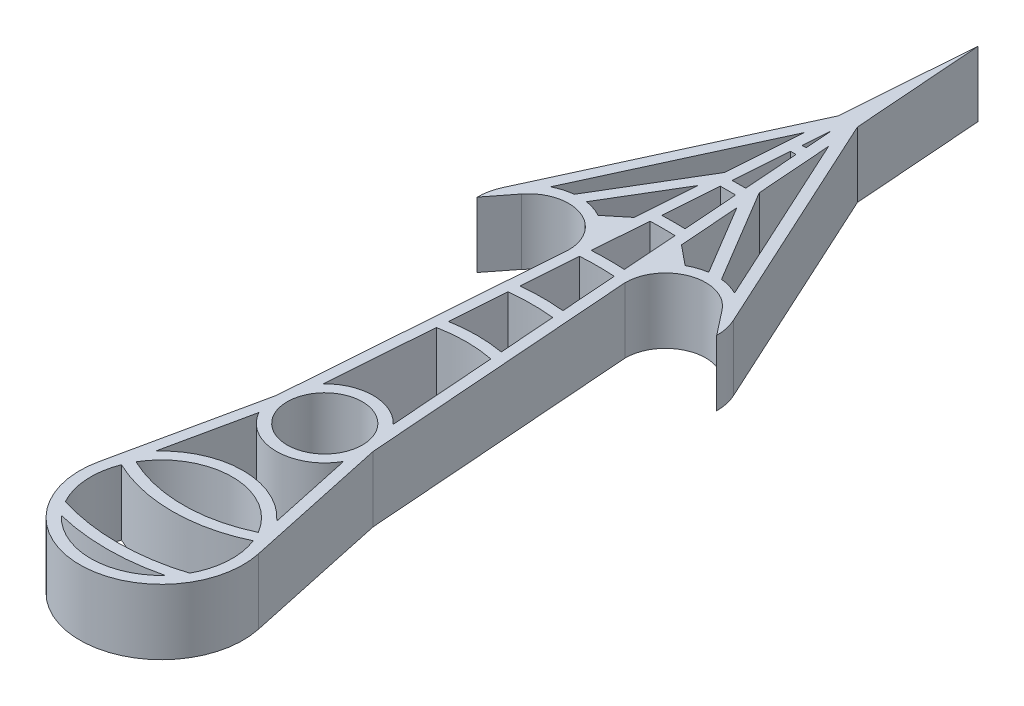
SolidWorks part; units mm, degrees
ref_plane "Front Plane" through (0, 0, 0) normal (0, 0, 1) x (1, 0, 0)
ref_plane "Top Plane" through (0, 0, 0) normal (0, 1, 0) x (1, 0, 0)
ref_plane "Right Plane" through (0, 0, 0) normal (1, 0, 0) x (0, 0, -1)
sketch "Sketch1" plane through (0, 0, 0) normal (0, 1, 0) x (1, 0, 0)
  line L0 (-4.45, 0) -> (0, 60)
  line L1 (0, 60) -> (4.45, 0)
  line L2 (0, 0) -> (0, 60) construction
  line L3 (0, 0) -> (0, -15) construction
  line L4 (-7.3328, -13.4254) -> (-4.45, 0)
  line L5 (4.45, 0) -> (7.3328, -13.4254)
  line L6 (-5.5696, -9.9771) -> (-3.8909, -2.1595)
  line L7 (3.8909, -2.1595) -> (5.5696, -9.9771)
  line L8 (3.45, 0) -> (4.45, 0) construction
  line L13 (-3.2194, 3.0721) -> (0, 46.4798)
  line L20 (0, 46.4798) -> (3.2194, 3.0721)
  circle A0 centre (0, 0) radius 3.45
  circle A2 centre (0, -15) radius 6.5
  arc A3 (5.5696, -9.9771) -> (-5.5696, -9.9771) centre (0, -15) ccw
  arc A8 (-3.8909, -2.1595) -> (3.8909, -2.1595) centre (0, 0) ccw
  arc A9 (3.2194, 3.0721) -> (-3.2194, 3.0721) centre (0, 0) ccw
  arc A11 (-7.3328, -13.4254) -> (7.3328, -13.4254) centre (0, -15) ccw
  circle A12 centre (0, -15) radius 7.5 construction
  point P32 (12.432, 3.8008)
  point P33 (0, 0)
  point P34 (18, 0)
  point P35 (0, 0)
  point P36 (13.3883, 4.0932)
  point P39 (0, 0)
  point P40 (23, 0)
  point P42 (0, 0)
  point P43 (19, 0)
  point P45 (28, 0)
  point P46 (0, 0)
  point P47 (24, 0)
  point P48 (0, 0)
  point P49 (33, 0)
  point P50 (0, 0)
  point P52 (0, 0)
  point P53 (38, 0)
  point P54 (0, 0)
  point P56 (0, 0)
  point P57 (43, 0)
  point P58 (0, 0)
  point P59 (39, 0)
  point P60 (0, 0)
  point P61 (48, 0)
  point P62 (0, 0)
  point P63 (44, 0)
  point P64 (0, 0)
  point P65 (53, 0)
  point P66 (0, 0)
  point P67 (49, 0)
  point P68 (0, 0)
  point P69 (58, 0)
  point P70 (0, 0)
  point P71 (54, 0)
  point P72 (0, 0)
  point P73 (63, 0)
  point P74 (0, 0)
  point P75 (59, 0)
  point P76 (64, 0)
  point P84 (10.5194, -26.7839)
  point P116 (34, 0)
  point P130 (29, 0)
  dimension "D1" = 6.9
  dimension "D3" = 4.45
  dimension "D4" = 15
  dimension "D5" = 1
  dimension "D6" = 13
  dimension "D11" = 4.45
  dimension "D2" = 60
  dimension "D7" = 1
  dimension "D8" = 1
  dimension "D10" = 1
  dimension "D9" = 4.45
extrude "Boss-Extrude1" add sketch "Sketch1" along normal blind 6
sketch "Sketch3" plane through (0, 0, 0) normal (0, 1, 0) x (1, 0, 0)
  line L0 (1.0216, 67.0139) -> (1.0956, 68.0123)
  line L1 (-0.6513, 62.021) -> (-0.5772, 61.0222)
  line L2 (0.5772, 61.0222) -> (0.6513, 62.021)
  line L4 (-3.718, 3.1091) -> (0, 53.2399)
  line L5 (0, 53.2399) -> (3.718, 3.1091)
  line L6 (-3.0107, 12.6466) -> (-2.9333, 13.6892)
  line L7 (-1.0956, 68.0123) -> (-1.0216, 67.0139)
  line L9 (5.9389, -18.048) -> (6.15, -19.031)
  line L10 (3.9611, -0.105) -> (6.844, -13.5304)
  line L11 (6.3718, -11.3314) -> (6.5909, -12.3515)
  line L12 (-6.7325, -12.2749) -> (-6.5008, -11.2578)
  line L13 (-6.1772, -19.0221) -> (-5.9542, -18.0429)
  line L15 (-0.2067, 56.0273) -> (-0.1326, 55.0281)
  line L16 (0.1326, 55.0281) -> (0.2067, 56.0273)
  line L17 (0.238, 50.0304) -> (0.3122, 49.0305)
  line L18 (-0.3122, 49.0305) -> (-0.238, 50.0304)
  line L19 (0.6831, 44.029) -> (0.7574, 43.0282)
  line L20 (-0.7574, 43.0282) -> (-0.6831, 44.029)
  line L21 (1.1288, 38.0208) -> (1.2031, 37.0186)
  line L22 (-1.2031, 37.0186) -> (-1.1288, 38.0208)
  line L23 (1.5751, 32.0021) -> (1.6496, 30.9975)
  line L24 (-1.6496, 30.9975) -> (-1.5751, 32.0021)
  line L25 (2.0229, 25.9654) -> (2.0977, 24.9566)
  line L26 (2.9333, 13.6892) -> (3.0107, 12.6466)
  line L27 (2.4767, 19.8461) -> (2.5522, 18.8278)
  line L28 (-2.0977, 24.9566) -> (-2.0229, 25.9654)
  line L29 (-2.5522, 18.8278) -> (-2.4767, 19.8461)
  arc A0 (-6.5008, -11.2578) -> (6.3718, -11.3314) centre (0, 0) ccw
  arc A1 (-6.7325, -12.2749) -> (6.5909, -12.3515) centre (0, 0) ccw
  arc A2 (-5.9542, -18.0429) -> (5.9389, -18.048) centre (0, 0) ccw
  arc A3 (-6.1772, -19.0221) -> (6.15, -19.031) centre (0, 0) ccw
  arc A10 (0.6831, 44.029) -> (-0.6831, 44.029) centre (0, 0) ccw
  arc A11 (0.7574, 43.0282) -> (-0.7574, 43.0282) centre (0, 0) ccw
  arc A20 (3.0107, 12.6466) -> (-3.0107, 12.6466) centre (0, 0) ccw
  circle A39 centre (0, 0) radius 20 construction
  circle A40 centre (0, 0) radius 19 construction
  circle A41 centre (0, 0) radius 14 construction
  circle A42 centre (0, 0) radius 13 construction
  arc A43 (2.9333, 13.6892) -> (-2.9333, 13.6892) centre (0, 0) ccw
  arc A44 (2.5522, 18.8278) -> (-2.5522, 18.8278) centre (0, 0) ccw
  arc A45 (2.4767, 19.8461) -> (-2.4767, 19.8461) centre (0, 0) ccw
  arc A46 (2.0977, 24.9566) -> (-2.0977, 24.9566) centre (0, 0) ccw
  arc A47 (2.0229, 25.9654) -> (-2.0229, 25.9654) centre (0, 0) ccw
  arc A48 (1.6496, 30.9975) -> (-1.6496, 30.9975) centre (0, 0) ccw
  arc A49 (1.5751, 32.0021) -> (-1.5751, 32.0021) centre (0, 0) ccw
  arc A50 (1.2031, 37.0186) -> (-1.2031, 37.0186) centre (0, 0) ccw
  arc A51 (1.1288, 38.0208) -> (-1.1288, 38.0208) centre (0, 0) ccw
  point P3 (12.432, 3.8008)
  point P8 (13.3883, 4.0932)
  point P10 (19, 0)
  point P12 (20, 0)
  point P14 (25, 0)
  point P16 (31, 0)
  point P18 (26, 0)
  point P20 (37, 0)
  point P22 (32, 0)
  point P24 (43, 0)
  point P26 (38, 0)
  point P27 (0, 0)
  point P28 (49, 0)
  point P29 (0, 0)
  point P30 (44, 0)
  point P31 (0, 0)
  point P32 (55, 0)
  point P33 (0, 0)
  point P34 (50, 0)
  point P35 (0, 0)
  point P36 (61, 0)
  point P37 (0, 0)
  point P38 (56, 0)
  point P39 (0, 0)
  point P40 (67, 0)
  point P41 (0, 0)
  point P42 (62, 0)
  point P43 (68, 0)
  dimension "D2" = 1
  dimension "D3" = 26
  dimension "D1" = 0.5
  dimension "D4" = 6
  dimension "D15" = 0.5
extrude "Boss-Extrude2" add sketch "Sketch3" along normal blind 6
sketch "Sketch5" plane through (0, 0, 0) normal (0, 1, 0) x (1, 0, 0)
  line L0 (11, 25) -> (9.2127, 27.2825)
  line L1 (5.6142, 29.6521) -> (1.2021, 37.0315)
  line L2 (0, 60) -> (4.45, 0) construction
  line L3 (1.0371, 39.2561) -> (6.7633, 29.679)
  line L4 (-0.1814, 44.0339) -> (0, 46.4798) construction
  line L5 (1.7499, 29.6451) -> (3.1543, 28.4968)
  line L6 (0.5014, 46.4798) -> (8.4513, 29.18)
  line L7 (0.2896, 49.3356) -> (10.5705, 26.9634)
  line L8 (8.431, 31.0202) -> (-1.1466, 31.0202) construction
  line L9 (0, 46.4798) -> (7.9605, 46.4798) construction
  line L10 (3.9962, 29.1002) -> (1.648, 31.0202)
  line L11 (-1.5189, 25.9998) -> (-1.1466, 31.0202) construction
  line L13 (1.5958, 25) -> (2.5958, 25)
  line L14 (0, 0) -> (0, 120.5281) construction
  line L16 (-0.4986, 59.963) -> (3.9514, -0.037)
  line L17 (-0.4986, 59.963) -> (3.9514, -0.037)
  line L21 (-0.7008, 37.0315) -> (9.1115, 37.0315) construction
  arc A0 (10, 25) -> (2.5958, 25) centre (6.2979, 25) ccw
  arc A1 (11, 25) -> (1.5958, 25) centre (6.2979, 25) ccw
  arc A2 (10, 25) -> (2.5958, 25) centre (6.2979, 25) ccw construction
  dimension "D1" = 10
  dimension "D3" = 1
  dimension "D4" = 1
  dimension "D5" = 1
  dimension "D7" = 25
  dimension "D2" = 1
  dimension "D6" = 0.5
extrude "Boss-Extrude4" add sketch "Sketch5" along normal blind 6 contours L0 A1 L17 L13 A0 | A1 L10 L17 L5 | A1 L3 L17 L1 | A1 L7 L17 L6 | A1 L5 L17
mirror "Mirror1" about plane through (0, 0, 0) normal (1, 0, 0) of "Boss-Extrude4"
